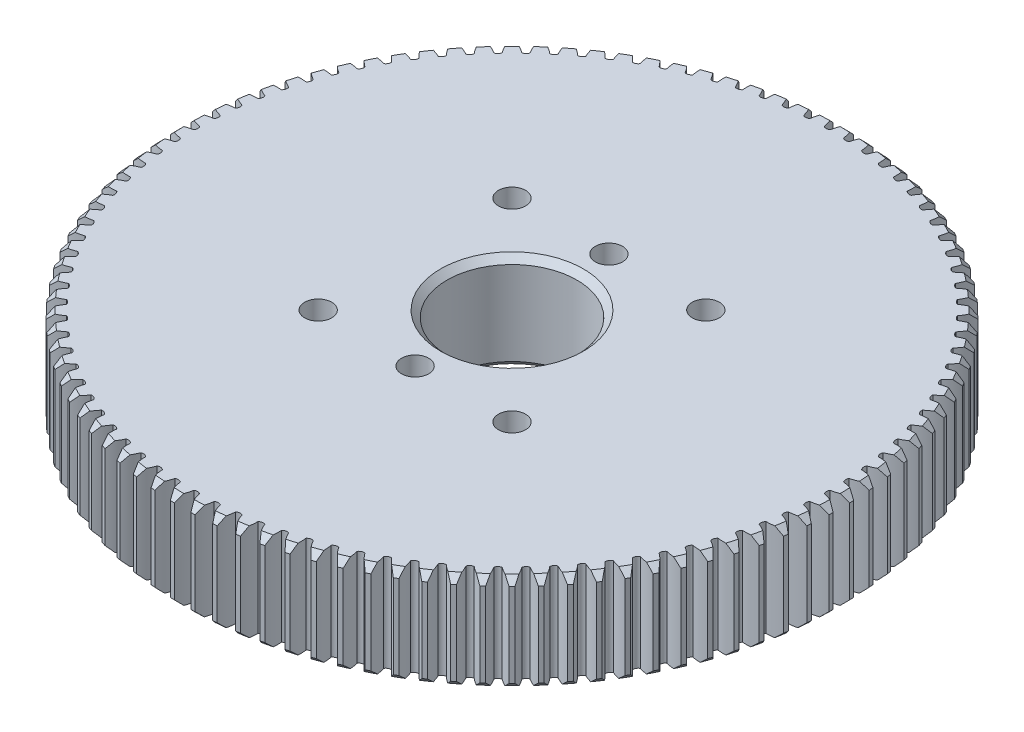
SolidWorks part; units mm, degrees
material "AISI 1045 鋼，冷拉"
ref_plane "Front Plane" through (0, 0, 0) normal (0, 0, 1) x (1, 0, 0)
ref_plane "Top Plane" through (0, 0, 0) normal (0, 1, 0) x (1, 0, 0)
ref_plane "Right Plane" through (0, 0, 0) normal (1, 0, 0) x (0, 0, -1)
sketch "草圖1" plane through (0, 0, 0) normal (0, 1, 0) x (1, 0, 0)
  circle A1 centre (0, 0) radius 51
  point P10 (0, 0)
  dimension "D2" = 102
extrude "填料-伸長1" add sketch "草圖1" along normal blind 15
sketch "草圖2" plane through (0, 15, 0) normal (0, 1, 0) x (1, 0, 0)
  line L3 (0, 0) -> (0, 51) construction
  arc A5 (-0.4579, 48.7831) -> (-1.2792, 50.984) centre (-7.1821, 47.5275) ccw
  arc A6 (0.4579, 48.7831) -> (1.2792, 50.984) centre (7.1821, 47.5275) cw
  arc A7 (1.2792, 50.984) -> (-1.2792, 50.984) centre (0, 0) ccw
  arc A8 (-0.4579, 48.7831) -> (0.4579, 48.7831) centre (0, 49.4872) ccw
  circle A17 centre (0, 0) radius 51 construction
  point P7 (0, 0)
  dimension "D1" = 6.8404
  dimension "D2" = 0.84
  dimension "D4" = 2.5585
  dimension "D3" = 7.9775
  dimension "D7" = 1.5128
extrude "除料-伸長1" cut sketch "草圖2" against normal through all
chamfer "導角1" distance 1 angle 45 2 edges at (0, 0, 51) (0, 15, 51)
pattern_circular "環狀複製排列1" count 100 over 360 about axis through (0, 0, 0) along (0, 1, 0) of "除料-伸長1"
sketch "草圖3" plane through (0, 0, 0) normal (0, -1, 0) x (1, 0, 0)
  circle A0 centre (0, 0) radius 10.05
  dimension "D1" = 20.1
extrude "除料-伸長2" cut sketch "草圖3" against normal through all
hole_wizard "M5x0.8 螺紋孔1" positions "草圖5" profile "草圖6" tap size "M5x0.8" standard "Ansi Metric"
sketch "草圖5" plane through (0, 15, 0) normal (0, 1, 0) x (1, 0, 0)
  line L0 (0, 0) -> (0, 15) construction
  point P1 (0, 15)
  dimension "D1" = 15
sketch "草圖6" plane through (0, 15, -15) normal (1, 0, 0) x (0, 0, 1)
  line L0 (0, 0) -> (0, 15)
  line L1 (0, 15) -> (2.1, 15)
  line L2 (2.1, 15) -> (2.1, 0)
  line L5 (2.1, 0) -> (0, 0)
  line L11 (0, -6.35) -> (0, 107.95) construction
  dimension "貫穿螺孔鑽直徑" = 4.2
  dimension "貫穿螺孔鑽深度" = 15
cosmetic thread "鑽孔螺紋1" parameters "D2"=5
pattern_linear "直線複製排列3" count 2 spacing 15 along (1, 0, 0) count 2 spacing 15 along (-1, 0, 0) of "M5x0.8 螺紋孔1"
pattern_linear "直線複製排列4" count 2 spacing 30 along (0, 0, 1) of "M5x0.8 螺紋孔1", "直線複製排列3"
chamfer "導角2" distance 1 angle 45 2 edges at (0, 0, -10.05) (0, 15, -10.05)
